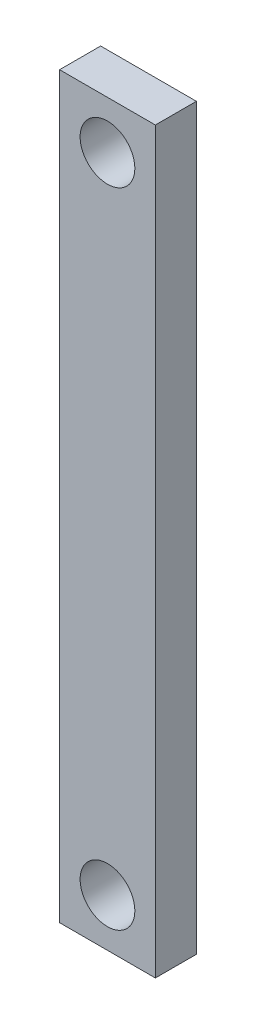
SolidWorks part; units mm, degrees
ref_plane "Front Plane" through (0, 0, 0) normal (0, 0, 1) x (1, 0, 0)
ref_plane "Top Plane" through (0, 0, 0) normal (0, 1, 0) x (1, 0, 0)
ref_plane "Right Plane" through (0, 0, 0) normal (1, 0, 0) x (0, 0, -1)
sketch "Sketch1" plane through (0, 0, 0) normal (0, 0, 1) x (1, 0, 0)
  line L0 (0, 0) -> (-35, 0)
  line L1 (-35, 0) -> (-35, -270)
  line L2 (-35, -270) -> (0, -270)
  line L3 (0, -270) -> (0, 0)
  dimension "D1" = 35
  dimension "D2" = 270
extrude "Boss-Extrude1" add sketch "Sketch1" along normal blind 15
sketch "Sketch2" plane through (0, 0, 15) normal (0, 0, 1) x (1, 0, 0)
  line L0 (-35, 0) -> (0, -35) construction
  line L1 (0, -270) -> (0, 0) construction
  line L2 (-35, -270) -> (0, -235) construction
  point P5 (-17.5, -17.5)
  point P10 (-17.5, -252.5)
  point P11 (-157.4941, -119.0429)
  dimension "D1" = 35
  dimension "D2" = 35
hole_wizard "Ø20.0mm Dowel Hole1" positions "Sketch3" profile "Sketch4" hole size "Ø20.0" standard "ISO" end condition through all
sketch "Sketch3" plane through (0, 0, 15) normal (0, 0, 1) x (1, 0, 0)
  point P0 (-17.5, -17.5)
  point P3 (-17.5, -252.5)
sketch "Sketch4" plane through (-17.5, -17.5, 15) normal (1, 0, 0) x (0, -1, 0)
  line L0 (0, 0) -> (0, 15)
  line L1 (0, 15) -> (10, 15)
  line L2 (10, 15) -> (10, 0)
  line L5 (10, 0) -> (0, 0)
  line L11 (0, -6.35) -> (0, 107.95) construction
  dimension "Thru Hole Dia." = 20
  dimension "Thru Hole Depth" = 15
